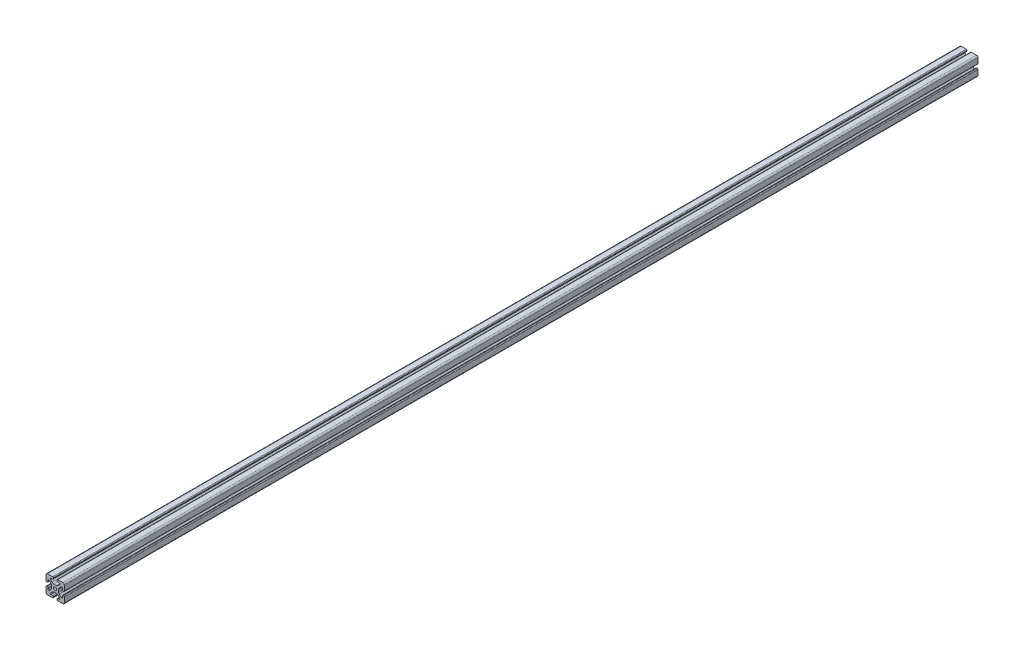
SolidWorks part; units mm, degrees
ref_plane "Front Plane" through (0, 0, 0) normal (0, 0, 1) x (1, 0, 0)
ref_plane "Top Plane" through (0, 0, 0) normal (0, 1, 0) x (1, 0, 0)
ref_plane "Right Plane" through (0, 0, 0) normal (1, 0, 0) x (0, 0, -1)
sketch "Sketch1" plane through (0, 0, 0) normal (0, 0, 1) x (1, 0, 0)
  line L0 (0, 19.7407) -> (0, -19.7407) construction
  line L1 (19.0335, 0) -> (-20.7246, 0) construction
  line L2 (-8.715, -15.5246) -> (-5.63, -15.5246)
  line L3 (-10.285, -13.9546) -> (-10.285, -13.4925)
  line L4 (-6.2171, -9.1098) -> (-10.0624, -12.9551)
  line L5 (2.7773, -7.685) -> (-2.7773, -7.685)
  line L6 (10.0624, -12.9551) -> (6.2171, -9.1098)
  line L7 (10.285, -13.9546) -> (10.285, -13.4925)
  line L8 (5.63, -15.5246) -> (8.715, -15.5246)
  line L9 (4.06, -18.43) -> (4.06, -17.0946)
  line L10 (-4.06, -18.43) -> (-4.06, -17.0946)
  line L11 (15.68, -8.7154) -> (15.68, -5.63)
  line L12 (-14.11, -10.2854) -> (-13.8169, -10.2854)
  line L13 (20, -16.83) -> (20, -5.63)
  line L14 (20, 5.63) -> (20, 13.0011)
  line L15 (-16.83, 20) -> (-5.63, 20)
  line L16 (5.63, 20) -> (12.9796, 20)
  line L17 (-8.715, 15.5246) -> (-5.63, 15.5246)
  line L18 (-20, -17.0184) -> (-20, -5.7579)
  line L19 (-20, 5.573) -> (-20, 13.0045)
  line L20 (-15.68, -8.7154) -> (-15.68, -5.7579)
  line L21 (-16.6746, -20) -> (-5.63, -20)
  line L22 (5.63, -20) -> (13, -20)
  line L23 (14.11, -10.2854) -> (13.6201, -10.2854)
  line L24 (13.1637, -9.947) -> (9.0762, -5.8595)
  line L25 (7.685, -2.5008) -> (7.685, 2.5008)
  line L26 (9.0762, 5.8595) -> (13.2795, 10.0628)
  line L27 (13.8169, 10.2854) -> (14.11, 10.2854)
  line L28 (15.68, 8.7154) -> (15.68, 5.63)
  line L29 (17.25, 4.06) -> (18.43, 4.06)
  line L30 (20, 13.0011) -> (20, 16.83)
  line L31 (16.83, 20) -> (12.9796, 20)
  line L32 (4.06, 18.43) -> (4.06, 17.0946)
  line L33 (5.63, 15.5246) -> (8.715, 15.5246)
  line L34 (10.285, 13.9546) -> (10.285, 13.4925)
  line L35 (10.0624, 12.9551) -> (6.2171, 9.1098)
  line L36 (2.7773, 7.685) -> (-2.7773, 7.685)
  line L37 (-6.2171, 9.1098) -> (-10.0624, 12.9551)
  line L38 (-10.285, 13.4925) -> (-10.285, 13.9546)
  line L39 (-4.06, 17.0946) -> (-4.06, 18.43)
  line L40 (-20, 16.83) -> (-20, 13.0045)
  line L41 (-18.43, 4.003) -> (-17.25, 4.003)
  line L42 (-15.68, 5.573) -> (-15.68, 8.4757)
  line L43 (-14.0552, 10.0447) -> (-13.7199, 10.033)
  line L44 (-13.0405, 9.8238) -> (-9.0762, 5.8595)
  line L45 (-7.685, 2.5008) -> (-7.685, -2.5008)
  line L46 (-9.0762, -5.8595) -> (-13.2795, -10.0628)
  line L47 (-17.2485, -4.1204) -> (-18.43, -4.1204)
  line L48 (13, -20) -> (16.83, -20)
  line L49 (18.43, -4.06) -> (17.25, -4.06)
  arc A0 (-5.63, -15.5246) -> (-4.06, -17.0946) centre (-5.63, -17.0946) cw
  arc A1 (-8.715, -15.5246) -> (-10.285, -13.9546) centre (-8.715, -13.9546) cw
  arc A2 (-10.285, -13.4925) -> (-10.0624, -12.9551) centre (-9.525, -13.4925) cw
  arc A3 (-6.2171, -9.1098) -> (-2.7773, -7.685) centre (-2.7773, -12.5496) cw
  arc A4 (2.7773, -7.685) -> (6.2171, -9.1098) centre (2.7773, -12.5496) cw
  arc A5 (10.0624, -12.9551) -> (10.285, -13.4925) centre (9.525, -13.4925) cw
  arc A6 (10.285, -13.9546) -> (8.715, -15.5246) centre (8.715, -13.9546) cw
  arc A7 (4.06, -17.0946) -> (5.63, -15.5246) centre (5.63, -17.0946) cw
  arc A8 (5.63, -20) -> (4.06, -18.43) centre (5.63, -18.43) cw
  arc A9 (-4.06, -18.43) -> (-5.63, -20) centre (-5.63, -18.43) cw
  circle A10 centre (0, 0) radius 3.4
  arc A11 (17.25, -4.06) -> (15.68, -5.63) centre (17.25, -5.63) ccw
  arc A12 (14.11, -10.2854) -> (15.68, -8.7154) centre (14.11, -8.7154) ccw
  arc A13 (13.1637, -9.947) -> (13.6201, -10.2854) centre (13.8117, -9.55) ccw
  arc A14 (7.685, -2.5008) -> (9.0762, -5.8595) centre (12.435, -2.5008) ccw
  arc A15 (9.0762, 5.8595) -> (7.685, 2.5008) centre (12.435, 2.5008) ccw
  arc A16 (13.8169, 10.2854) -> (13.2795, 10.0628) centre (13.8169, 9.5254) ccw
  arc A17 (15.68, 8.7154) -> (14.11, 10.2854) centre (14.11, 8.7154) ccw
  arc A18 (15.68, 5.63) -> (17.25, 4.06) centre (17.25, 5.63) ccw
  arc A19 (18.43, 4.06) -> (20, 5.63) centre (18.43, 5.63) ccw
  arc A20 (20, 16.83) -> (16.83, 20) centre (16.83, 16.83) ccw
  arc A21 (5.63, 20) -> (4.06, 18.43) centre (5.63, 18.43) ccw
  arc A22 (4.06, 17.0946) -> (5.63, 15.5246) centre (5.63, 17.0946) ccw
  arc A23 (10.285, 13.9546) -> (8.715, 15.5246) centre (8.715, 13.9546) ccw
  arc A24 (10.0624, 12.9551) -> (10.285, 13.4925) centre (9.525, 13.4925) ccw
  arc A25 (2.7773, 7.685) -> (6.2171, 9.1098) centre (2.7773, 12.5496) ccw
  arc A26 (-6.2171, 9.1098) -> (-2.7773, 7.685) centre (-2.7773, 12.5496) ccw
  arc A27 (-10.285, 13.4925) -> (-10.0624, 12.9551) centre (-9.525, 13.4925) ccw
  arc A28 (-8.715, 15.5246) -> (-10.285, 13.9546) centre (-8.715, 13.9546) ccw
  arc A29 (-5.63, 15.5246) -> (-4.06, 17.0946) centre (-5.63, 17.0946) ccw
  arc A30 (-4.06, 18.43) -> (-5.63, 20) centre (-5.63, 18.43) ccw
  arc A31 (-16.83, 20) -> (-20, 16.83) centre (-16.83, 16.83) ccw
  arc A32 (-20, 5.573) -> (-18.43, 4.003) centre (-18.43, 5.573) ccw
  arc A33 (-17.25, 4.003) -> (-15.68, 5.573) centre (-17.25, 5.573) ccw
  arc A34 (-14.0552, 10.0447) -> (-15.68, 8.4757) centre (-14.11, 8.4757) ccw
  arc A35 (-13.0405, 9.8238) -> (-13.7199, 10.033) centre (-13.5779, 9.2864) ccw
  arc A36 (-7.685, 2.5008) -> (-9.0762, 5.8595) centre (-12.435, 2.5008) ccw
  arc A37 (-9.0762, -5.8595) -> (-7.685, -2.5008) centre (-12.435, -2.5008) ccw
  arc A38 (-13.8169, -10.2854) -> (-13.2795, -10.0628) centre (-13.8169, -9.5254) ccw
  arc A39 (-15.68, -8.7154) -> (-14.11, -10.2854) centre (-14.11, -8.7154) ccw
  arc A40 (-15.68, -5.7579) -> (-17.2485, -4.1204) centre (-17.2485, -5.6904) ccw
  arc A41 (-18.43, -4.1204) -> (-20, -5.7579) centre (-18.4315, -5.6904) ccw
  arc A42 (-20, -17.0184) -> (-16.6746, -20) centre (-16.8354, -16.8341) ccw
  arc A43 (16.83, -20) -> (20, -16.83) centre (16.83, -16.83) ccw
  arc A44 (20, -5.63) -> (18.43, -4.06) centre (18.43, -5.63) ccw
  dimension "D1" = 6.8
  dimension "D2" = 4.32
  dimension "D3" = 15.37
  dimension "D4" = 20.57
  dimension "D5" = 15.37
  dimension "D6" = 40
  dimension "D7" = 20
  dimension "D8" = 4.32
  dimension "D9" = 8.12
extrude "Boss-Extrude1" add sketch "Sketch1" along normal blind 2000
